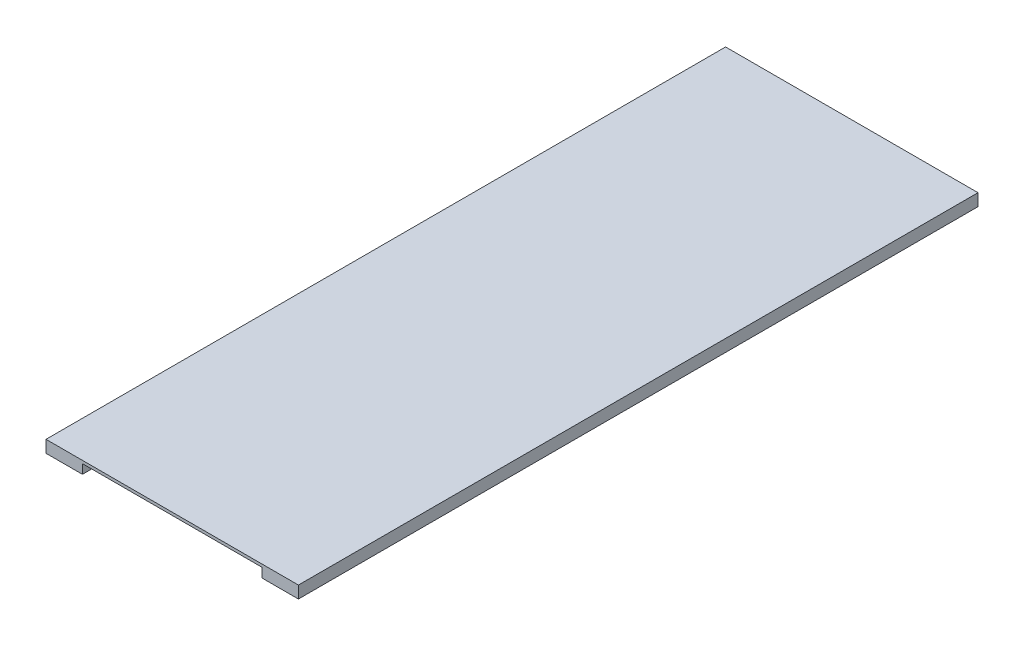
SolidWorks part; units mm, degrees
ref_plane "Front Plane" through (0, 0, 0) normal (0, 0, 1) x (1, 0, 0)
ref_plane "Top Plane" through (0, 0, 0) normal (0, 1, 0) x (1, 0, 0)
ref_plane "Right Plane" through (0, 0, 0) normal (1, 0, 0) x (0, 0, -1)
sketch "Sketch1" plane through (0, 0, 0) normal (0, 0, 1) x (1, 0, 0)
  line L0 (-15, -3.8281) -> (-15, 1.1719)
  line L1 (-15, 1.1719) -> (89, 1.1719)
  line L2 (89, 1.1719) -> (89, -3.8281)
  line L3 (-15, -3.8281) -> (0, -3.8281)
  line L4 (0, -3.8281) -> (0, 0)
  line L5 (0, 0) -> (74, 0)
  line L6 (74, 0) -> (74, -3.8281)
  line L7 (74, -3.8281) -> (89, -3.8281)
  dimension "D1" = 5
  dimension "D2" = 5
  dimension "D3" = 104
  dimension "D4" = 15
  dimension "D5" = 15
extrude "Boss-Extrude1" add sketch "Sketch1" along normal blind 280
